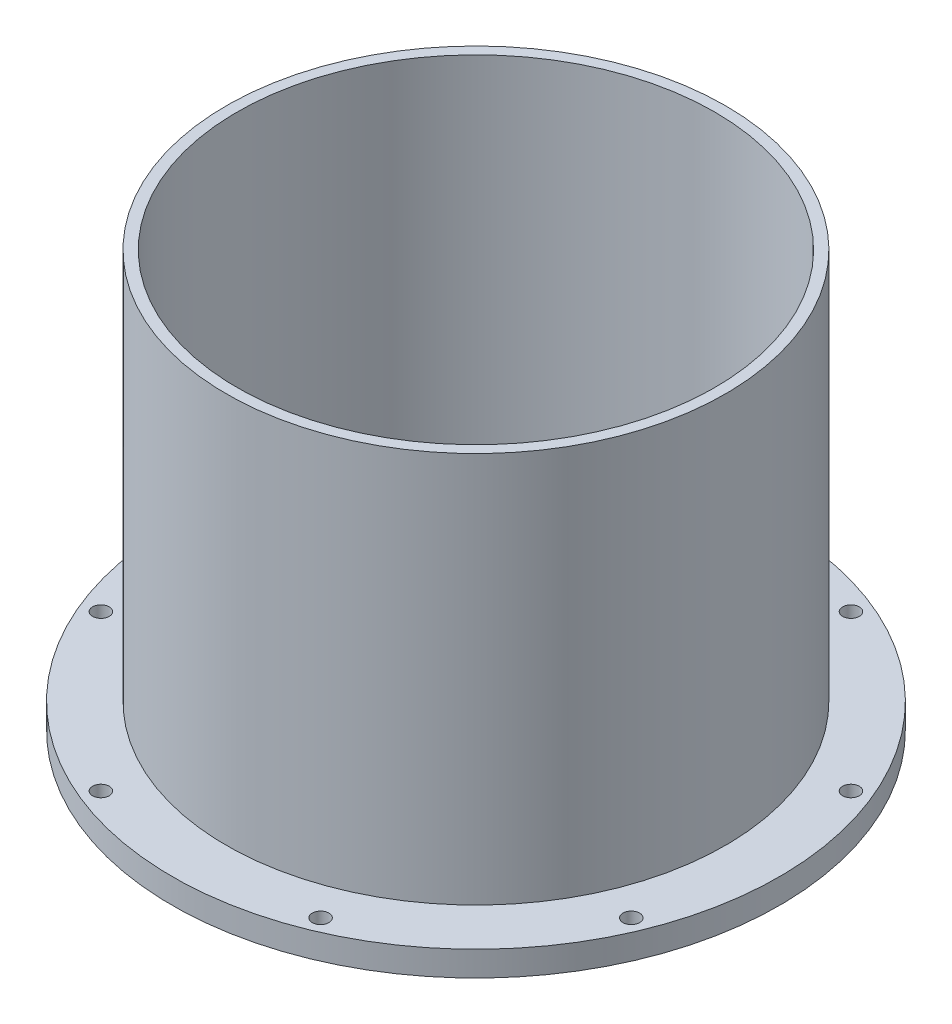
SolidWorks part; units mm, degrees
ref_plane "정면" through (0, 0, 0) normal (0, 0, 1) x (1, 0, 0)
ref_plane "평면" through (0, 0, 0) normal (0, 1, 0) x (1, 0, 0)
ref_plane "우측면" through (0, 0, 0) normal (1, 0, 0) x (0, 0, -1)
sketch "스케치1" plane through (0, 0, 0) normal (0, 0, 1) x (1, 0, 0)
  line L0 (0, 0) -> (0, 250) construction
sketch "스케치2" plane through (0, 0, 0) normal (0, 0, 1) x (1, 0, 0)
  line L1 (-182.5, 0) -> (-182.5, 15)
  line L2 (-143.5, 0) -> (-182.5, 0)
  line L3 (-150, 250) -> (-143.5, 250)
  line L5 (-143.5, 0) -> (-143.5, 250)
  line L6 (-150, 15) -> (-150, 250)
  line L9 (-150, 15) -> (-182.5, 15)
  point P0 (0, 0)
  point P14 (-152.6272, 128.5086)
  dimension "D1" = 143.5
  dimension "D2" = 150
  dimension "D3" = 182.5
  dimension "D4" = 15
  dimension "D5" = 250
revolve "회전1" add sketch "스케치2" angle 360 about L0
sketch "스케치3" plane through (0, 0, 0) normal (0, 1, 0) x (1, 0, 0)
  line L0 (0, 0) -> (159.3692, 66.0129) construction
  line L1 (0, 0) -> (172.5, 0) construction
  circle A0 centre (0, 0) radius 172.5 construction
  circle A1 centre (159.3692, 66.0129) radius 5
  dimension "D1" = 345
  dimension "D3" = 10
  dimension "D2" = 22.5
extrude "컷-돌출1" cut sketch "스케치3" along normal up to next (15 mm away)
pattern_circular "원형 패턴1" count 8 over 360 about axis through (0, 0, 0) along (0, 1, 0) of "컷-돌출1"
